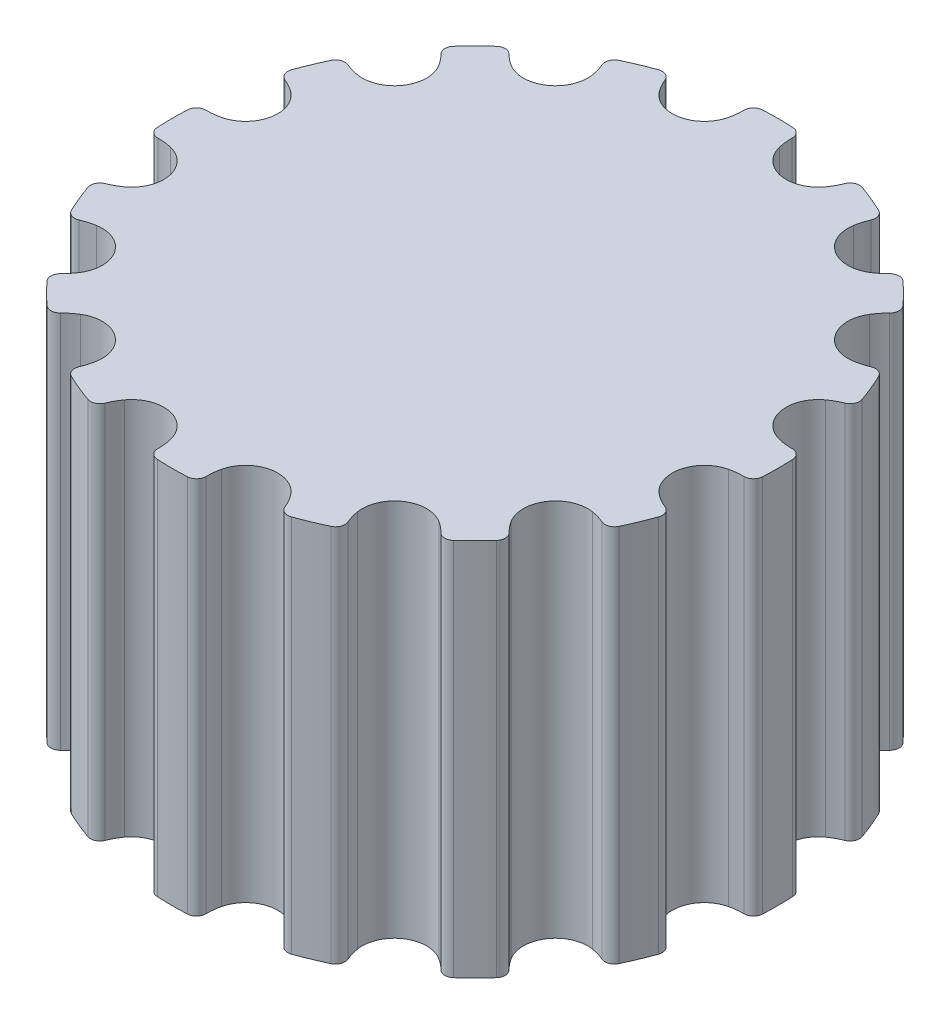
SolidWorks part; units mm, degrees
ref_plane "Front Plane" through (0, 0, 0) normal (0, 0, 1) x (1, 0, 0)
ref_plane "Top Plane" through (0, 0, 0) normal (0, 1, 0) x (1, 0, 0)
ref_plane "Right Plane" through (0, 0, 0) normal (1, 0, 0) x (0, 0, -1)
sketch "Sketch1" plane through (0, 0, 0) normal (0, 1, 0) x (1, 0, 0)
  line L0 (0, 0) -> (0, 8) construction
  line L1 (0, 0) -> (1.5607, 7.8463) construction
  arc A0 (-0.3992, 7.99) -> (0.3992, 7.99) centre (0, 0) cw
  arc A1 (0.3992, 7.99) -> (0.6367, 7.7367) centre (0.3867, 7.7403) cw
  arc A2 (0.6367, 7.7367) -> (0.6765, 7.368) centre (2.1565, 7.7147) ccw
  arc A3 (0.6765, 7.368) -> (1.3383, 6.7282) centre (1.5041, 7.5619) ccw
  arc A4 (-0.6367, 7.7367) -> (-0.6765, 7.368) centre (-2.1565, 7.7147) cw
  arc A5 (-0.6765, 7.368) -> (-1.3383, 6.7282) centre (-1.5041, 7.5619) cw
  arc A6 (-0.3992, 7.99) -> (-0.6367, 7.7367) centre (-0.3867, 7.7403) ccw
  arc A7 (2.1946, 7.0661) -> (1.3383, 6.7282) centre (1.5041, 7.5619) cw
  arc A8 (2.3725, 7.3914) -> (2.1946, 7.0661) centre (0.9599, 7.9527) cw
  arc A9 (2.6889, 7.5346) -> (2.3725, 7.3914) centre (2.6049, 7.2991) ccw
  arc A10 (2.6889, 7.5346) -> (3.4264, 7.2291) centre (0, 0) cw
  arc A11 (3.4264, 7.2291) -> (3.5489, 6.9042) centre (3.3193, 7.0032) cw
  arc A12 (3.5489, 6.9042) -> (3.4447, 6.5482) centre (4.9446, 6.3022) ccw
  arc A13 (3.4447, 6.5482) -> (3.8112, 5.7039) centre (4.2834, 6.4106) ccw
  arc A14 (4.7316, 5.6884) -> (3.8112, 5.7039) centre (4.2834, 6.4106) cw
  arc A15 (5.0205, 5.9209) -> (4.7316, 5.6884) centre (3.9302, 6.98) cw
  arc A16 (5.3676, 5.9321) -> (5.0205, 5.9209) centre (5.1998, 5.7467) ccw
  arc A17 (5.3676, 5.9321) -> (5.9321, 5.3676) centre (0, 0) cw
  arc A18 (5.9321, 5.3676) -> (5.9209, 5.0205) centre (5.7467, 5.1998) cw
  arc A19 (5.9209, 5.0205) -> (5.6884, 4.7316) centre (6.98, 3.9302) ccw
  arc A20 (5.6884, 4.7316) -> (5.7039, 3.8112) centre (6.4106, 4.2834) ccw
  arc A21 (6.5482, 3.4447) -> (5.7039, 3.8112) centre (6.4106, 4.2834) cw
  arc A22 (6.9042, 3.5489) -> (6.5482, 3.4447) centre (6.3022, 4.9446) cw
  arc A23 (7.2291, 3.4264) -> (6.9042, 3.5489) centre (7.0032, 3.3193) ccw
  arc A24 (7.2291, 3.4264) -> (7.5346, 2.6889) centre (0, 0) cw
  arc A25 (7.5346, 2.6889) -> (7.3914, 2.3725) centre (7.2991, 2.6049) cw
  arc A26 (7.3914, 2.3725) -> (7.0661, 2.1946) centre (7.9527, 0.9599) ccw
  arc A27 (7.0661, 2.1946) -> (6.7282, 1.3383) centre (7.5619, 1.5041) ccw
  arc A28 (7.368, 0.6765) -> (6.7282, 1.3383) centre (7.5619, 1.5041) cw
  arc A29 (7.7367, 0.6367) -> (7.368, 0.6765) centre (7.7147, 2.1565) cw
  arc A30 (7.99, 0.3992) -> (7.7367, 0.6367) centre (7.7403, 0.3867) ccw
  arc A31 (7.99, 0.3992) -> (7.99, -0.3992) centre (0, 0) cw
  arc A32 (7.99, -0.3992) -> (7.7367, -0.6367) centre (7.7403, -0.3867) cw
  arc A33 (7.7367, -0.6367) -> (7.368, -0.6765) centre (7.7147, -2.1565) ccw
  arc A34 (7.368, -0.6765) -> (6.7282, -1.3383) centre (7.5619, -1.5041) ccw
  arc A35 (7.0661, -2.1946) -> (6.7282, -1.3383) centre (7.5619, -1.5041) cw
  arc A36 (7.3914, -2.3725) -> (7.0661, -2.1946) centre (7.9527, -0.9599) cw
  arc A37 (7.5346, -2.6889) -> (7.3914, -2.3725) centre (7.2991, -2.6049) ccw
  arc A38 (7.5346, -2.6889) -> (7.2291, -3.4264) centre (0, 0) cw
  arc A39 (7.2291, -3.4264) -> (6.9042, -3.5489) centre (7.0032, -3.3193) cw
  arc A40 (6.9042, -3.5489) -> (6.5482, -3.4447) centre (6.3022, -4.9446) ccw
  arc A41 (6.5482, -3.4447) -> (5.7039, -3.8112) centre (6.4106, -4.2834) ccw
  arc A42 (5.6884, -4.7316) -> (5.7039, -3.8112) centre (6.4106, -4.2834) cw
  arc A43 (5.9209, -5.0205) -> (5.6884, -4.7316) centre (6.98, -3.9302) cw
  arc A44 (5.9321, -5.3676) -> (5.9209, -5.0205) centre (5.7467, -5.1998) ccw
  arc A45 (5.9321, -5.3676) -> (5.3676, -5.9321) centre (0, 0) cw
  arc A46 (5.3676, -5.9321) -> (5.0205, -5.9209) centre (5.1998, -5.7467) cw
  arc A47 (5.0205, -5.9209) -> (4.7316, -5.6884) centre (3.9302, -6.98) ccw
  arc A48 (4.7316, -5.6884) -> (3.8112, -5.7039) centre (4.2834, -6.4106) ccw
  arc A49 (3.4447, -6.5482) -> (3.8112, -5.7039) centre (4.2834, -6.4106) cw
  arc A50 (3.5489, -6.9042) -> (3.4447, -6.5482) centre (4.9446, -6.3022) cw
  arc A51 (3.4264, -7.2291) -> (3.5489, -6.9042) centre (3.3193, -7.0032) ccw
  arc A52 (3.4264, -7.2291) -> (2.6889, -7.5346) centre (0, 0) cw
  arc A53 (2.6889, -7.5346) -> (2.3725, -7.3914) centre (2.6049, -7.2991) cw
  arc A54 (2.3725, -7.3914) -> (2.1946, -7.0661) centre (0.9599, -7.9527) ccw
  arc A55 (2.1946, -7.0661) -> (1.3383, -6.7282) centre (1.5041, -7.5619) ccw
  arc A56 (0.6765, -7.368) -> (1.3383, -6.7282) centre (1.5041, -7.5619) cw
  arc A57 (0.6367, -7.7367) -> (0.6765, -7.368) centre (2.1565, -7.7147) cw
  arc A58 (0.3992, -7.99) -> (0.6367, -7.7367) centre (0.3867, -7.7403) ccw
  arc A59 (0.3992, -7.99) -> (-0.3992, -7.99) centre (0, 0) cw
  arc A60 (-0.3992, -7.99) -> (-0.6367, -7.7367) centre (-0.3867, -7.7403) cw
  arc A61 (-0.6367, -7.7367) -> (-0.6765, -7.368) centre (-2.1565, -7.7147) ccw
  arc A62 (-0.6765, -7.368) -> (-1.3383, -6.7282) centre (-1.5041, -7.5619) ccw
  arc A63 (-2.1946, -7.0661) -> (-1.3383, -6.7282) centre (-1.5041, -7.5619) cw
  arc A64 (-2.3725, -7.3914) -> (-2.1946, -7.0661) centre (-0.9599, -7.9527) cw
  arc A65 (-2.6889, -7.5346) -> (-2.3725, -7.3914) centre (-2.6049, -7.2991) ccw
  arc A66 (-2.6889, -7.5346) -> (-3.4264, -7.2291) centre (0, 0) cw
  arc A67 (-3.4264, -7.2291) -> (-3.5489, -6.9042) centre (-3.3193, -7.0032) cw
  arc A68 (-3.5489, -6.9042) -> (-3.4447, -6.5482) centre (-4.9446, -6.3022) ccw
  arc A69 (-3.4447, -6.5482) -> (-3.8112, -5.7039) centre (-4.2834, -6.4106) ccw
  arc A70 (-4.7316, -5.6884) -> (-3.8112, -5.7039) centre (-4.2834, -6.4106) cw
  arc A71 (-5.0205, -5.9209) -> (-4.7316, -5.6884) centre (-3.9302, -6.98) cw
  arc A72 (-5.3676, -5.9321) -> (-5.0205, -5.9209) centre (-5.1998, -5.7467) ccw
  arc A73 (-5.3676, -5.9321) -> (-5.9321, -5.3676) centre (0, 0) cw
  arc A74 (-5.9321, -5.3676) -> (-5.9209, -5.0205) centre (-5.7467, -5.1998) cw
  arc A75 (-5.9209, -5.0205) -> (-5.6884, -4.7316) centre (-6.98, -3.9302) ccw
  arc A76 (-5.6884, -4.7316) -> (-5.7039, -3.8112) centre (-6.4106, -4.2834) ccw
  arc A77 (-6.5482, -3.4447) -> (-5.7039, -3.8112) centre (-6.4106, -4.2834) cw
  arc A78 (-6.9042, -3.5489) -> (-6.5482, -3.4447) centre (-6.3022, -4.9446) cw
  arc A79 (-7.2291, -3.4264) -> (-6.9042, -3.5489) centre (-7.0032, -3.3193) ccw
  arc A80 (-7.2291, -3.4264) -> (-7.5346, -2.6889) centre (0, 0) cw
  arc A81 (-7.5346, -2.6889) -> (-7.3914, -2.3725) centre (-7.2991, -2.6049) cw
  arc A82 (-7.3914, -2.3725) -> (-7.0661, -2.1946) centre (-7.9527, -0.9599) ccw
  arc A83 (-7.0661, -2.1946) -> (-6.7282, -1.3383) centre (-7.5619, -1.5041) ccw
  arc A84 (-7.368, -0.6765) -> (-6.7282, -1.3383) centre (-7.5619, -1.5041) cw
  arc A85 (-7.7367, -0.6367) -> (-7.368, -0.6765) centre (-7.7147, -2.1565) cw
  arc A86 (-7.99, -0.3992) -> (-7.7367, -0.6367) centre (-7.7403, -0.3867) ccw
  arc A87 (-7.99, -0.3992) -> (-7.99, 0.3992) centre (0, 0) cw
  arc A88 (-7.99, 0.3992) -> (-7.7367, 0.6367) centre (-7.7403, 0.3867) cw
  arc A89 (-7.7367, 0.6367) -> (-7.368, 0.6765) centre (-7.7147, 2.1565) ccw
  arc A90 (-7.368, 0.6765) -> (-6.7282, 1.3383) centre (-7.5619, 1.5041) ccw
  arc A91 (-7.0661, 2.1946) -> (-6.7282, 1.3383) centre (-7.5619, 1.5041) cw
  arc A92 (-7.3914, 2.3725) -> (-7.0661, 2.1946) centre (-7.9527, 0.9599) cw
  arc A93 (-7.5346, 2.6889) -> (-7.3914, 2.3725) centre (-7.2991, 2.6049) ccw
  arc A94 (-7.5346, 2.6889) -> (-7.2291, 3.4264) centre (0, 0) cw
  arc A95 (-7.2291, 3.4264) -> (-6.9042, 3.5489) centre (-7.0032, 3.3193) cw
  arc A96 (-6.9042, 3.5489) -> (-6.5482, 3.4447) centre (-6.3022, 4.9446) ccw
  arc A97 (-6.5482, 3.4447) -> (-5.7039, 3.8112) centre (-6.4106, 4.2834) ccw
  arc A98 (-5.6884, 4.7316) -> (-5.7039, 3.8112) centre (-6.4106, 4.2834) cw
  arc A99 (-5.9209, 5.0205) -> (-5.6884, 4.7316) centre (-6.98, 3.9302) cw
  arc A100 (-5.9321, 5.3676) -> (-5.9209, 5.0205) centre (-5.7467, 5.1998) ccw
  arc A101 (-5.9321, 5.3676) -> (-5.3676, 5.9321) centre (0, 0) cw
  arc A102 (-5.3676, 5.9321) -> (-5.0205, 5.9209) centre (-5.1998, 5.7467) cw
  arc A103 (-5.0205, 5.9209) -> (-4.7316, 5.6884) centre (-3.9302, 6.98) ccw
  arc A104 (-4.7316, 5.6884) -> (-3.8112, 5.7039) centre (-4.2834, 6.4106) ccw
  arc A105 (-3.4447, 6.5482) -> (-3.8112, 5.7039) centre (-4.2834, 6.4106) cw
  arc A106 (-3.5489, 6.9042) -> (-3.4447, 6.5482) centre (-4.9446, 6.3022) cw
  arc A107 (-3.4264, 7.2291) -> (-3.5489, 6.9042) centre (-3.3193, 7.0032) ccw
  arc A108 (-3.4264, 7.2291) -> (-2.6889, 7.5346) centre (0, 0) cw
  arc A109 (-2.6889, 7.5346) -> (-2.3725, 7.3914) centre (-2.6049, 7.2991) cw
  arc A110 (-2.3725, 7.3914) -> (-2.1946, 7.0661) centre (-0.9599, 7.9527) ccw
  arc A111 (-2.1946, 7.0661) -> (-1.3383, 6.7282) centre (-1.5041, 7.5619) ccw
  point P230 (0, 0)
  dimension "D3" = 0.25
  dimension "D4" = 1.52
  dimension "D6" = 0.85
  dimension "D2" = 11.25
  dimension "D5" = 0.61
  dimension "D7" = 1.14
  dimension "D1" = 8
  dimension "D8" = 16
extrude "Boss-Extrude1" add sketch "Sketch1" along normal blind 10 contours A111 A110 A109 A108 A107 A106 A105 A104 A103 A102 A101 A100 A99 A98 A97 A96 A95 A94 A93 A92 A91 A90 A89 A88 A87 A86 A85 A84 A83 A82 A81 A80 A79 A78 A77 A76 A75 A74 A73 A72 A71 A70 A69 A68 A67 A66 A65 A64 A63 A62 A61
equation "\"teeth\"= 16"
equation "\"pitchdiameter\"= \"teeth\""
equation "\"circumference\"= \"pitchdiameter\" * pi"
equation "\"toothangle\"= 360 / \"teeth\""
equation "\"D2@Sketch1\"=\"toothangle\"/2"
equation "\"D1@Sketch1\"=\"pitchdiameter\"/2"
